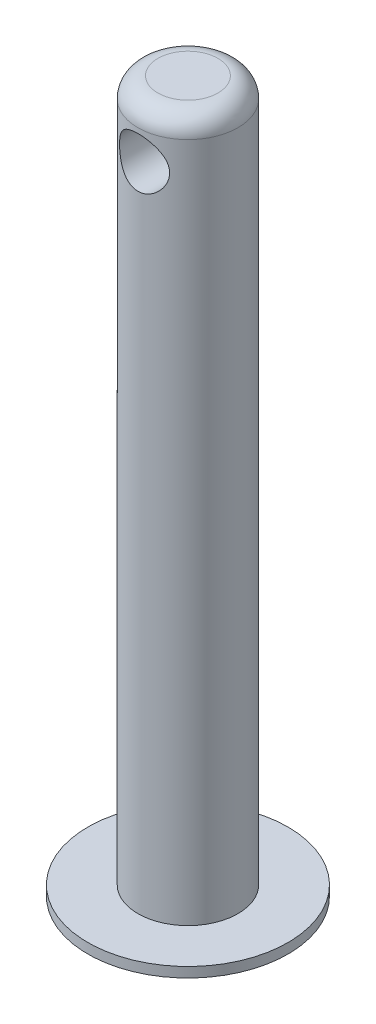
SolidWorks part; units mm, degrees
ref_plane "Piano frontale" through (0, 0, 0) normal (0, 0, 1) x (1, 0, 0)
ref_plane "Piano superiore" through (0, 0, 0) normal (0, 1, 0) x (1, 0, 0)
ref_plane "Piano destro" through (0, 0, 0) normal (1, 0, 0) x (0, 0, -1)
sketch "Schizzo1" plane through (0, 0, 0) normal (0, 1, 0) x (1, 0, 0)
  circle A0 centre (0, 0) radius 5
  dimension "D1" = 10
extrude "Estrusione-Estrusione1" add sketch "Schizzo1" along normal blind 70
fillet "Raccordo1" radius 2 1 edges at (0, 70, 5)
sketch "Schizzo2" plane through (0, 0, 0) normal (0, 0, 1) x (1, 0, 0)
  line L0 (3, 70) -> (-3, 70) construction
  circle A0 centre (0, 65) radius 2.5
  dimension "D1" = 5
  dimension "D2" = 5
extrude "Taglio-Estrusione1" cut sketch "Schizzo2" against normal through all both and the other way through all contours A0
sketch "Schizzo3" plane through (0, 0, 0) normal (0, -1, 0) x (-1, 0, 0)
  circle A0 centre (0, 0) radius 10
  dimension "D1" = 20
extrude "Estrusione-Estrusione2" add sketch "Schizzo3" along normal blind 1
